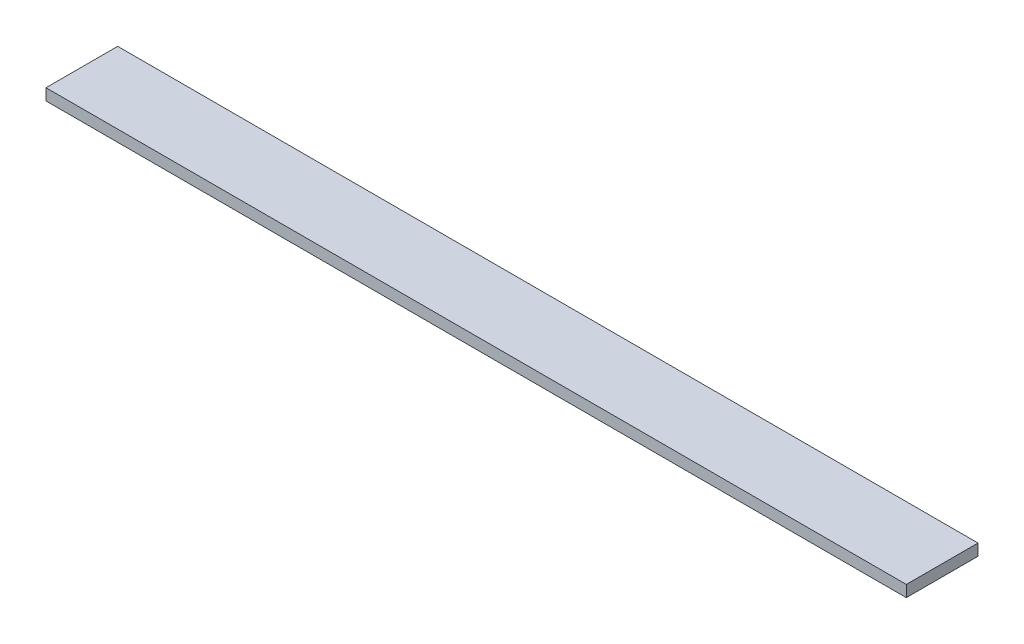
SolidWorks part; units mm, degrees
ref_plane "Спереди" through (0, 0, 0) normal (0, 0, 1) x (1, 0, 0)
ref_plane "Сверху" through (0, 0, 0) normal (0, 1, 0) x (1, 0, 0)
ref_plane "Справа" through (0, 0, 0) normal (1, 0, 0) x (0, 0, -1)
sketch "Эскиз1" plane through (0, 0, 0) normal (0, 1, 0) x (1, 0, 0)
  line L1 (-300, 25) -> (300, 25)
  line L2 (-300, 25) -> (-300, -25)
  line L3 (-300, -25) -> (300, -25)
  line L4 (300, 25) -> (300, -25)
  line L5 (-300, 25) -> (300, -25) construction
  line L6 (-300, -25) -> (300, 25) construction
  point P0 (0, 0)
extrude "Бобышка-Вытянуть1" add sketch "Эскиз1" along normal blind 8
